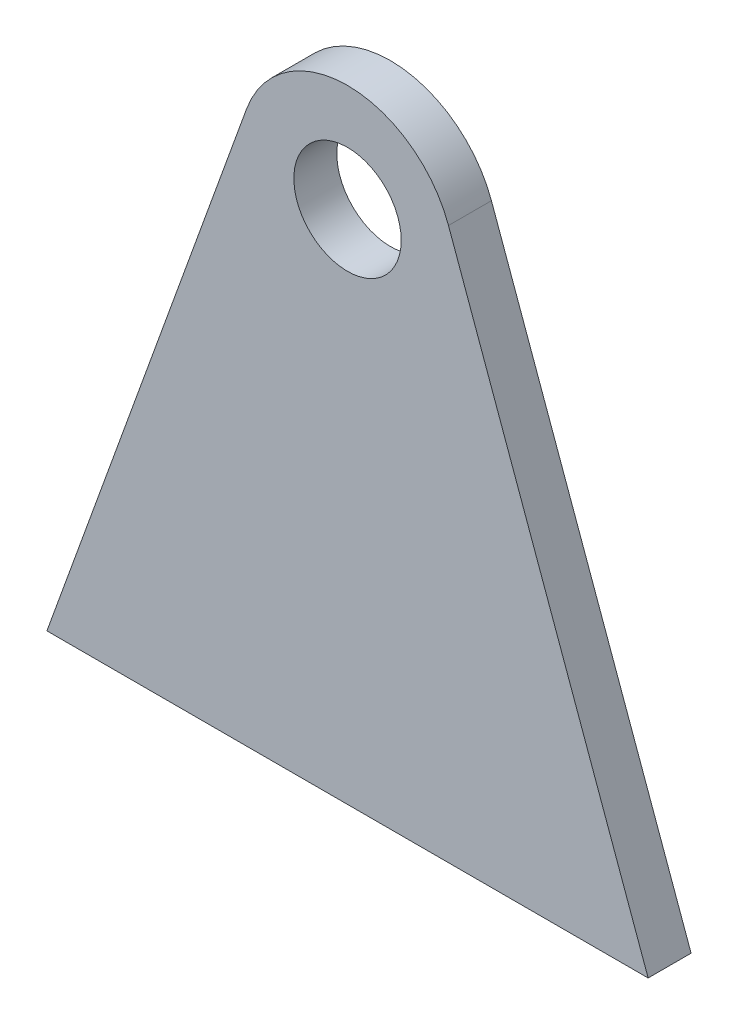
SolidWorks part; units mm, degrees
ref_plane "Front Plane" through (0, 0, 0) normal (0, 0, 1) x (1, 0, 0)
ref_plane "Top Plane" through (0, 0, 0) normal (0, 1, 0) x (1, 0, 0)
ref_plane "Right Plane" through (0, 0, 0) normal (1, 0, 0) x (0, 0, -1)
sketch "Sketch1" plane through (0, 0, 0) normal (0, 0, 1) x (1, 0, 0)
  line L0 (0, 0) -> (280, 0)
  line L1 (140, 0) -> (140, 240) construction
  line L2 (0, 0) -> (92.9824, 257.0102)
  line L3 (280, 0) -> (187.0176, 257.0102)
  circle A0 centre (140, 240) radius 25
  arc A1 (187.0176, 257.0102) -> (92.9824, 257.0102) centre (140, 240) ccw
  dimension "D2" = 50
  dimension "D3" = 100
  dimension "D1" = 280
  dimension "D4" = 240
extrude "Boss-Extrude1" add sketch "Sketch1" along normal blind 20
